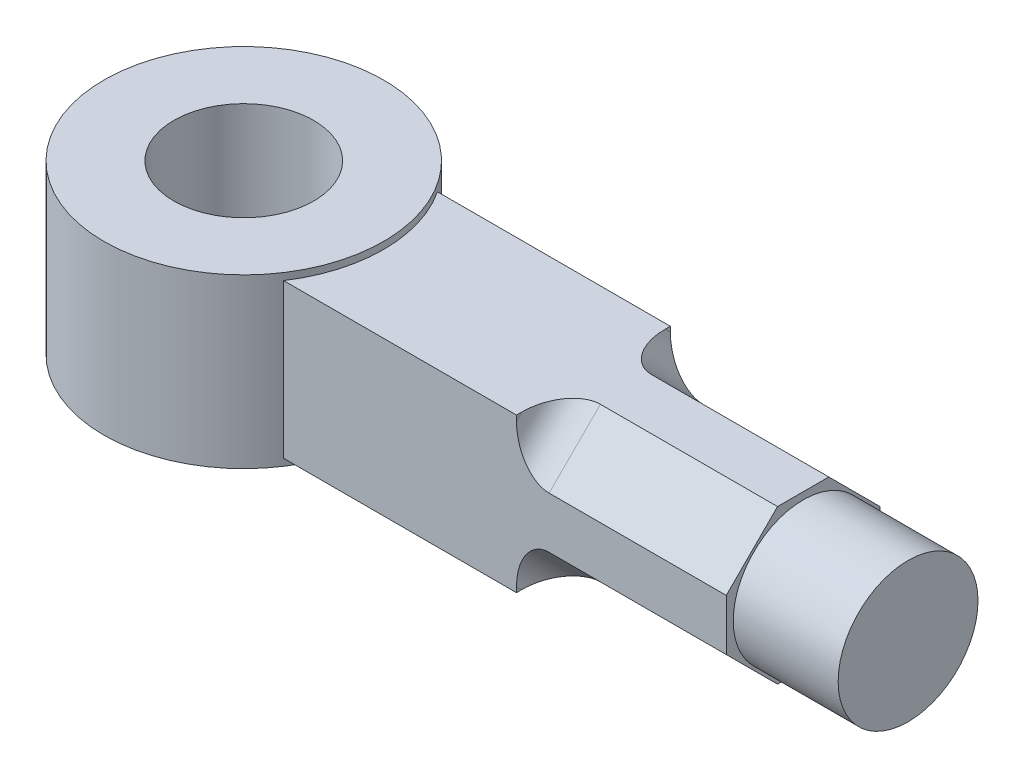
SolidWorks part; units mm, degrees
ref_plane "Front Plane" through (0, 0, 0) normal (0, 0, 1) x (1, 0, 0)
ref_plane "Top Plane" through (0, 0, 0) normal (0, 1, 0) x (1, 0, 0)
ref_plane "Right Plane" through (0, 0, 0) normal (1, 0, 0) x (0, 0, -1)
sketch "Sketch1" plane through (0, 0, 0) normal (0, 1, 0) x (1, 0, 0)
  circle A0 centre (0, 0) radius 15
  circle A1 centre (0, 0) radius 30
  dimension "D1" = 30
  dimension "D2" = 60
extrude "Boss-Extrude1" add sketch "Sketch1" against normal blind 36
ref_plane "Plane1" through (0, -18, 0) normal (0, 1, 0) x (1, 0, 0)
sketch "Sketch2" plane through (0, -18, 0) normal (0, 1, 0) x (1, 0, 0)
  line L1 (25.0549, 16.5) -> (120, 16.5)
  line L2 (25.0549, 16.5) -> (25.0549, -16.5)
  line L3 (25.0549, -16.5) -> (120, -16.5)
  line L4 (120, 16.5) -> (120, -16.5)
  circle A0 centre (0, 0) radius 30 construction
  point P6 (0, 0)
  dimension "D1" = 33
  dimension "D2" = 120
extrude "Boss-Extrude2" add sketch "Sketch2" along normal mid plane 33
sketch "Sketch3" plane through (120, 0, 0) normal (1, 0, 0) x (0, 0, -1)
  line L0 (5.5, -1.5) -> (16.5, -12.5)
  line L1 (16.5, -1.5) -> (-16.5, -1.5) construction
  line L2 (16.5, -1.5) -> (16.5, -34.5) construction
  line L3 (16.5, -12.5) -> (16.5, -1.5)
  line L4 (16.5, -1.5) -> (5.5, -1.5)
  line L5 (33, -18) -> (-33, -18) construction
  line L6 (16.5, -34.5) -> (16.5, -23.5)
  line L7 (16.5, -23.5) -> (5.5, -34.5)
  line L8 (5.5, -34.5) -> (16.5, -34.5)
  line L9 (-16.5, -34.5) -> (-5.5, -34.5)
  line L10 (-5.5, -34.5) -> (-16.5, -23.5)
  line L11 (-16.5, -23.5) -> (-16.5, -34.5)
  line L12 (-16.5, -1.5) -> (-16.5, -12.5)
  line L13 (-16.5, -12.5) -> (-5.5, -1.5)
  line L14 (-5.5, -1.5) -> (-16.5, -1.5)
  point P6 (0, -18)
  point P9 (0, -18)
  point P12 (0, 0)
  point P26 (0, -18)
  dimension "D1" = 11
  dimension "D2" = 11
  dimension "D3" = 4
extrude "Cut-Extrude1" cut sketch "Sketch3" against normal blind 45
fillet "Fillet1" radius 7 4 edges at (75, -29, 11) (75, -29, -11) (75, -7, 11) (75, -7, -11)
sketch "Sketch4" plane through (120, 0, 0) normal (1, 0, 0) x (0, 0, -1)
  circle A0 centre (0, -18) radius 15
  point P2 (0, 0)
  dimension "D1" = 30
extrude "Boss-Extrude3" add sketch "Sketch4" along normal mid plane 45
